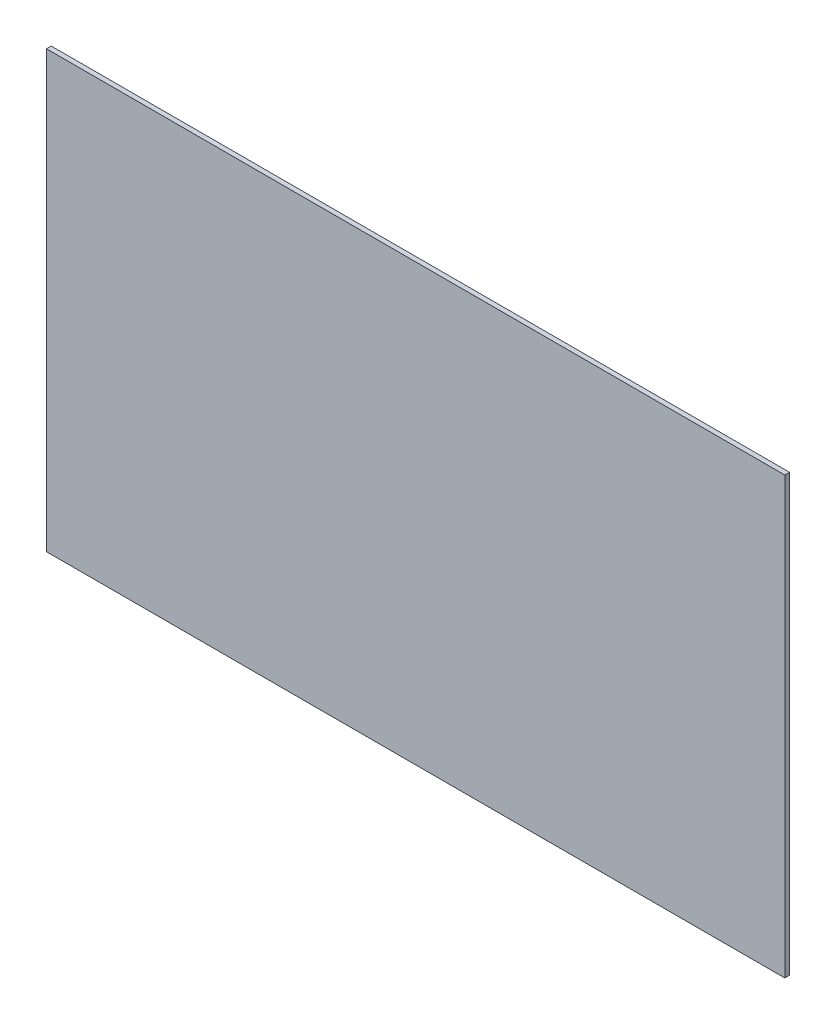
SolidWorks part; units mm, degrees
material "Plastique personnalisé"
ref_plane "Plan de face" through (0, 0, 0) normal (0, 0, 1) x (1, 0, 0)
ref_plane "Plan de dessus" through (0, 0, 0) normal (0, 1, 0) x (1, 0, 0)
ref_plane "Plan de droite" through (0, 0, 0) normal (1, 0, 0) x (0, 0, -1)
sketch "Esquisse1" plane through (0, 0, 0) normal (0, 0, 1) x (1, 0, 0)
  line L1 (-125, -73.75) -> (125, -73.75)
  line L2 (-125, -73.75) -> (-125, 73.75)
  line L3 (-125, 73.75) -> (125, 73.75)
  line L4 (125, -73.75) -> (125, 73.75)
  line L5 (-125, -73.75) -> (125, 73.75) construction
  line L6 (-125, 73.75) -> (125, -73.75) construction
  point P0 (0, 0)
  dimension "D1" = 147.5
  dimension "D2" = 250
extrude "Boss.-Extru.1" add sketch "Esquisse1" along normal blind 1.6
ref_plane "Plan1" through (0, 0, 0) normal (1, 0, 0) x (0, 0, -1)
ref_plane "Sagit2" through (0, 0, 0) normal (0, 1, 0) x (1, 0, 0)
